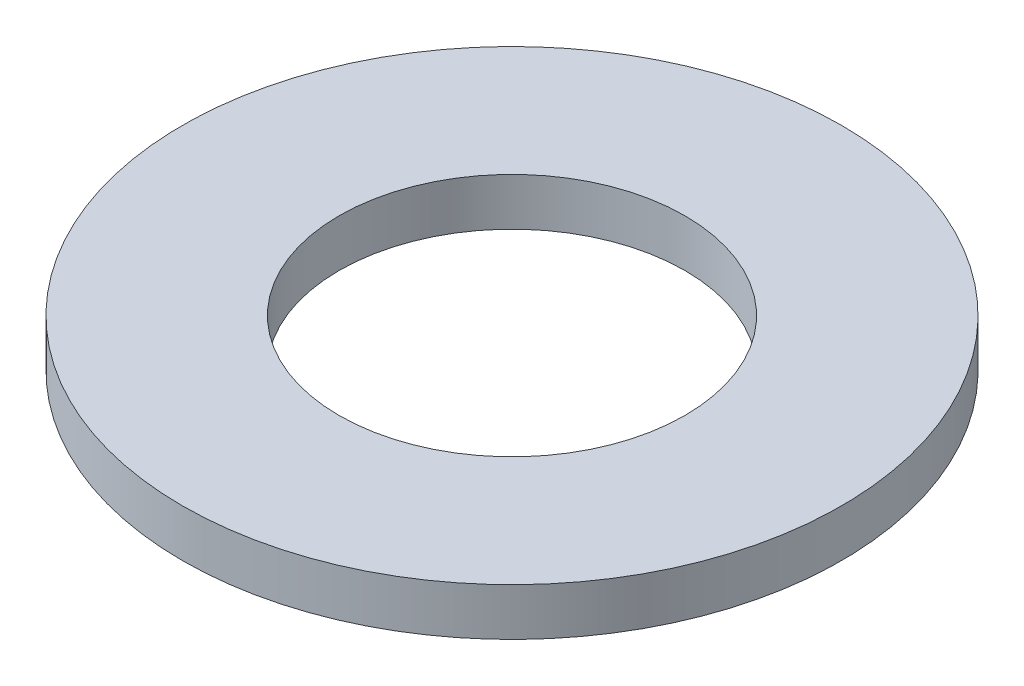
SolidWorks part; units mm, degrees
ref_plane "Front" through (0, 0, 0) normal (0, 0, 1) x (1, 0, 0)
ref_plane "Top" through (0, 0, 0) normal (0, 1, 0) x (1, 0, 0)
ref_plane "Right" through (0, 0, 0) normal (1, 0, 0) x (0, 0, -1)
ref_plane "Plane1" through (0, 0, 0) normal (0, 0, -1) x (-1, 0, 0)
sketch "Sketch1" plane through (0, 0, 0) normal (0, 0, -1) x (-1, 0, 0)
  line L0 (-8.3312, 2.286) -> (-15.875, 2.286)
  line L1 (-15.875, 2.286) -> (-15.875, 0)
  line L2 (-15.875, 0) -> (-8.3312, 0)
  line L3 (-8.3312, 0) -> (-8.3312, 2.286)
  line L4 (0, 0) -> (0, 2.286) construction
revolve "Revolve1" add sketch "Sketch1" angle 360 about L4
